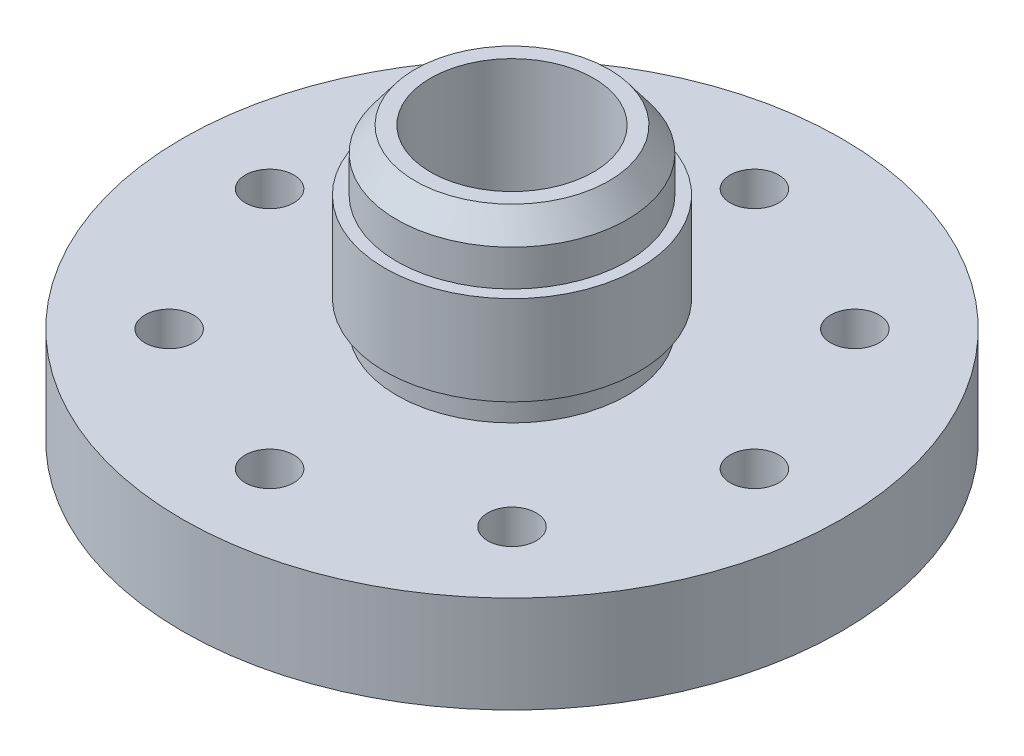
SolidWorks part; units mm, degrees
ref_plane "Front Plane" through (0, 0, 0) normal (0, 0, 1) x (1, 0, 0)
ref_plane "Top Plane" through (0, 0, 0) normal (0, 1, 0) x (1, 0, 0)
ref_plane "Right Plane" through (0, 0, 0) normal (1, 0, 0) x (0, 0, -1)
sketch "Sketch1" plane through (0, 0, 0) normal (0, 1, 0) x (1, 0, 0)
  circle A0 centre (0, 0) radius 43.18
  dimension "D1" = 86.36
extrude "flange extrude" add sketch "Sketch1" along normal blind 12.7
sketch "Sketch2" plane through (0, 12.7, 0) normal (0, 1, 0) x (1, 0, 0)
  circle A0 centre (0, 0) radius 15.0876
  dimension "D1" = 30.1752
extrude "an fitting body" add sketch "Sketch2" along normal blind 23.114 contours A0
sketch "Sketch3" plane through (0, 35.814, 0) normal (0, 1, 0) x (1, 0, 0)
  circle A0 centre (0, 0) radius 10.668
  dimension "D1" = 21.336
extrude "hole for fitting" cut sketch "Sketch3" against normal up to next
ref_plane "Plane1" through (0, 16.1798, 0) normal (0, 1, 0) x (1, 0, 0)
sketch "Sketch5" plane through (0, 16.1798, 0) normal (0, 1, 0) x (1, 0, 0)
  circle A0 centre (0, 0) radius 16.637
  circle A3 centre (0, 0) radius 15.0876 construction
  circle A4 centre (0, 0) radius 15.0876
  dimension "D1" = 33.274
extrude "meat for thread" add sketch "Sketch5" along normal blind 11.7094
sketch "Sketch6" plane through (0, 0, 0) normal (0, 0, 1) x (1, 0, 0)
  line L0 (12.6873, 35.814) -> (15.0876, 32.6287)
  line L1 (15.0876, 35.814) -> (-15.0876, 35.814) construction
  line L2 (15.0876, 27.8892) -> (15.0876, 35.814) construction
  line L3 (15.0876, 32.6287) -> (15.0876, 35.814)
  line L4 (15.0876, 35.814) -> (12.6873, 35.814)
  dimension "D1" = 2.4003
  dimension "D2" = 37
ref_axis "Axis1" through (0, 0, 0) along (0, 1, 0)
revolve "Cut-Revolve1" cut sketch "Sketch6" angle 360 about axis through (0, 0, 0) along (0, 1, 0)
sketch "Sketch10" plane through (0, 0, 0) normal (0, -1, 0) x (1, 0, 0)
  circle A0 centre (0, 0) radius 12.7
  circle A1 centre (0, 0) radius 15.1892
  dimension "D1" = 25.4
  dimension "D2" = 2.4892
extrude "O-ring groove" cut sketch "Sketch10" against normal blind 1.2624
sketch "Sketch13" plane through (0, 0, 0) normal (0, -1, 0) x (1, 0, 0)
  line L0 (0, 0) -> (0, 31.75) construction
  circle A0 centre (0, 31.75) radius 3.175
  point P4 (0, 31.75)
  dimension "D2" = 6.35
  dimension "D1" = 31.75
extrude "bolt hole" cut sketch "Sketch13" against normal up to next (12.7 mm away) contours A0
pattern_circular "CirPattern1" count 8 every 45 about axis through (0, 0, 0) along (0, 1, 0) of "bolt hole"
equation "\"flange_radius\"= 1.7in'radius of part"
equation "\"D1@Sketch1\" = 2 * \"flange_radius\""
equation "\"O_ring_ID\"= 1in'inner diameter of o-ring"
equation "\"O_ring_CS\"= .07in'cross section radius of o-ring"
equation "\"D2@Sketch10\"=\"O_ring_CS\"*1.4"
equation "\"D1@O-ring groove\"=\"O_ring_CS\"*.71"
equation "\"bolt_radius\"= 1.25in'radius at which bolt holes are located"
equation "\"D1@Sketch13\"=\"bolt_radius\""
equation "\"bolt_hole_size\" = .25in'radius for bolt holes"
equation "\"bolts\"= 8'number of bolts"
equation "\"D2@Sketch13\"=\"bolt_hole_size\""
equation "\"D2@CirPattern1\"=360/\"bolts\""
equation "\"D1@CirPattern1\"=\"bolts\""
